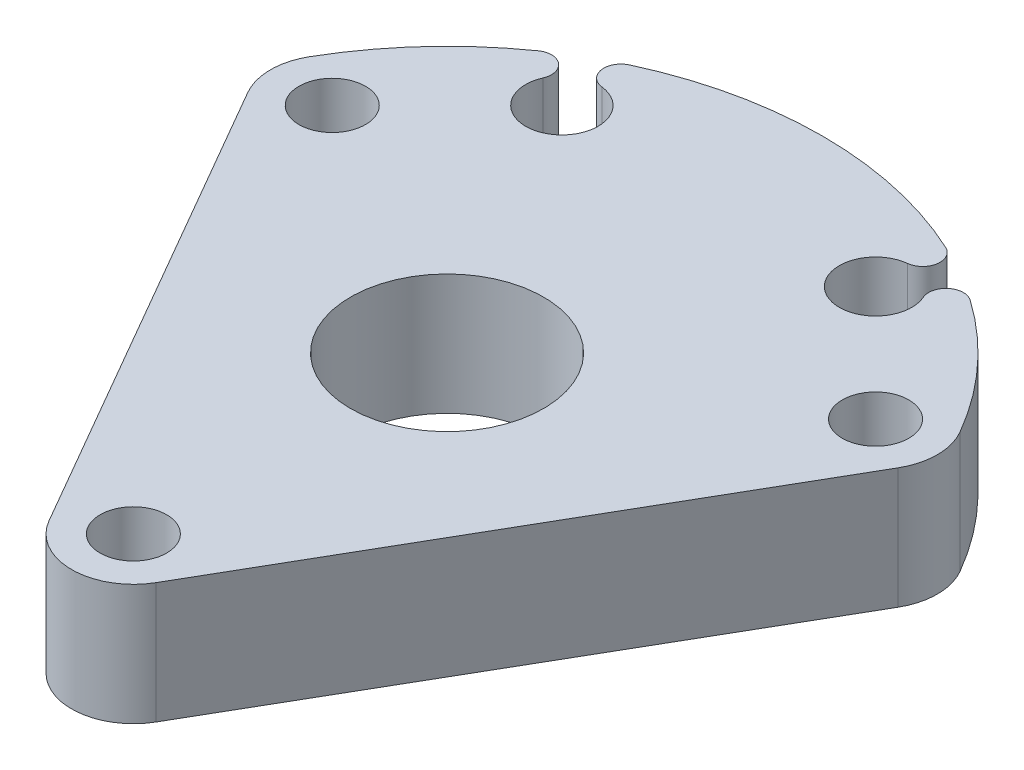
SolidWorks part; units mm, degrees
material "Cedar"
ref_plane "Front Plane" through (0, 0, 0) normal (0, 0, 1) x (1, 0, 0)
ref_plane "Top Plane" through (0, 0, 0) normal (0, 1, 0) x (1, 0, 0)
ref_plane "Right Plane" through (0, 0, 0) normal (1, 0, 0) x (0, 0, -1)
sketch "Sketch1" plane through (0, 0, 0) normal (0, 1, 0) x (1, 0, 0)
  line L0 (0, 16.5) -> (-14.2894, 8.25) construction
  line L1 (-14.2894, 8.25) -> (-14.2894, -8.25) construction
  line L2 (-17.104, 6.625) -> (-2.8146, -18.125)
  line L3 (2.8146, -18.125) -> (17.104, 6.625)
  arc A0 (17.104, 9.875) -> (-17.104, 9.875) centre (0, 0) ccw
  circle A1 centre (0, 0) radius 16.5 construction
  circle A2 centre (0, 0) radius 5.08
  circle A3 centre (0, 16.5) radius 1.75 construction
  circle A4 centre (-14.2894, 8.25) radius 1.75
  circle A5 centre (-14.2894, -8.25) radius 1.75 construction
  circle A6 centre (0, -16.5) radius 1.75
  circle A7 centre (14.2894, -8.25) radius 1.75 construction
  circle A8 centre (14.2894, 8.25) radius 1.75
  arc A9 (-17.104, 9.875) -> (-17.104, 6.625) centre (-14.2894, 8.25) ccw
  arc A10 (17.104, 6.625) -> (17.104, 9.875) centre (14.2894, 8.25) ccw
  arc A11 (-2.8146, -18.125) -> (2.8146, -18.125) centre (0, -16.5) ccw
  dimension "D1" = 39.5
  dimension "D2" = 33
  dimension "D3" = 10.16
  dimension "D4" = 3.5
extrude "Boss-Extrude1" add sketch "Sketch1" along normal blind 6.35
sketch "Sketch2" plane through (0, 6.35, 0) normal (0, 1, 0) x (1, 0, 0)
  line L0 (0, 0) -> (0, 15.7203) construction
  line L1 (7.1447, 12.375) -> (0, 0) construction
  line L2 (0, 0) -> (3.7596, 6.5118) construction
  arc A0 (8.0362, 16.1824) -> (9.9963, 15.0507) centre (8.25, 14.2894) ccw
  circle A1 centre (0, 0) radius 19.75 construction
  arc A2 (11.3546, 16.1597) -> (8.3174, 17.9132) centre (0, 0) ccw
  arc A3 (11.3546, 16.1597) -> (9.9963, 15.0507) centre (10.831, 15.4146) ccw
  arc A4 (8.3174, 17.9132) -> (8.0362, 16.1824) centre (7.9339, 17.0873) cw
  dimension "D2" = 3.81
  dimension "D3" = 1.524
  dimension "D1" = 16.5
  dimension "D6" = 30
extrude "Cut-Extrude1" cut sketch "Sketch2" against normal through all
pattern_circular "CirPattern1" count 2 every 60 about axis through (0, 0, 0) along (0, 1, 0) of "Cut-Extrude1"
